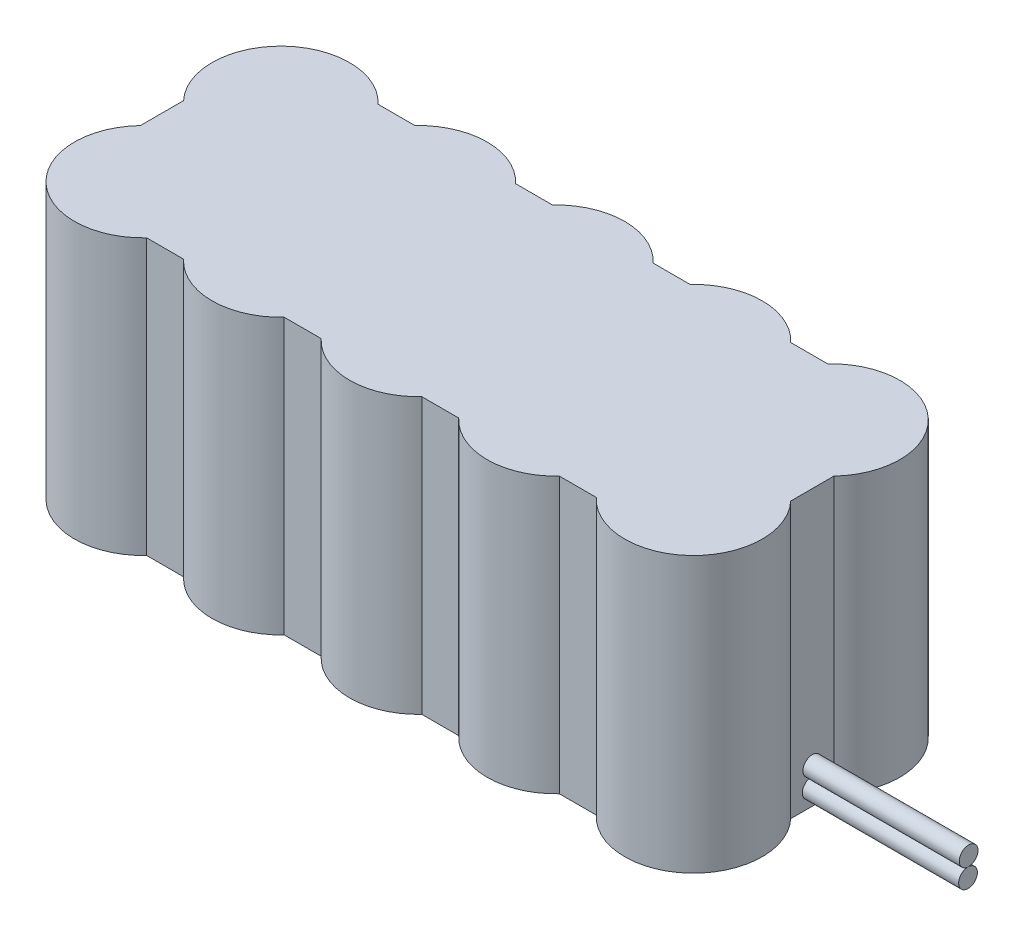
SolidWorks part; units mm, degrees
ref_plane "Front Plane" through (0, 0, 0) normal (0, 0, 1) x (1, 0, 0)
ref_plane "Top Plane" through (0, 0, 0) normal (0, 1, 0) x (1, 0, 0)
ref_plane "Right Plane" through (0, 0, 0) normal (1, 0, 0) x (0, 0, -1)
sketch "Sketch1" plane through (0, 0, 0) normal (0, 1, 0) x (1, 0, 0)
  circle A0 centre (0, 0) radius 11
  circle A1 centre (22, 0) radius 11
  circle A2 centre (44, 0) radius 11
  circle A3 centre (66, 0) radius 11
  circle A4 centre (88, 0) radius 11
  circle A5 centre (0, 22) radius 11
  circle A6 centre (22, 22) radius 11
  circle A7 centre (44, 22) radius 11
  circle A8 centre (66, 22) radius 11
  circle A9 centre (88, 22) radius 11
  dimension "D1" = 22
  dimension "D2" = 22
  dimension "D4" = 22
  dimension "D5" = 22
  dimension "D8" = 22
  dimension "D10" = 22
  dimension "D12" = 22
  dimension "D13" = 22
  dimension "D14" = 22
  dimension "D15" = 22
  dimension "D3" = 22
  dimension "D6" = 22
  dimension "D7" = 22
  dimension "D9" = 22
  dimension "D11" = 22
extrude "Extrude1" add sketch "Sketch1" along normal blind 44 contours A5 | A6 | A7 | A8 | A9 | A4 | A3 | A2 | A1 | A0
sketch "Sketch2" plane through (0, 44, 0) normal (0, 1, 0) x (1, 0, 0)
  line L1 (-8, 29.5) -> (96, 29.5)
  line L2 (-8, 29.5) -> (-8, -7.5)
  line L3 (-8, -7.5) -> (96, -7.5)
  line L4 (96, 29.5) -> (96, -7.5)
  circle A0 centre (0, 22) radius 11 construction
  circle A2 centre (88, 0) radius 11 construction
  dimension "D3" = 8
  dimension "D1" = 7.5
  dimension "D2" = 7.5
  dimension "D4" = 8
extrude "Extrude7" add sketch "Sketch2" against normal blind 44
sketch "Sketch4" plane through (96, 0, 0) normal (1, 0, 0) x (0, 0, -1)
  circle A1 centre (11, 5.6393) radius 1.5
  dimension "D2" = 3
extrude "Extrude12" add sketch "Sketch4" along normal blind 25
sketch "Sketch5" plane through (96, 0, 0) normal (1, 0, 0) x (0, 0, -1)
  circle A0 centre (10.9048, 2.6393) radius 1.5
  circle A1 centre (11, 5.6393) radius 1.5 construction
  dimension "D1" = 3
  dimension "D2" = 3
extrude "Extrude14" add sketch "Sketch5" along normal blind 25 separate body
sketch "Sketch6" plane through (0, 44, 0) normal (0, 1, 0) x (1, 0, 0)
  line L0 (-8, 11) -> (96, 11) construction
  line L1 (-8, 14.4502) -> (-8, 7.5498) construction
  line L2 (96, 7.5498) -> (96, 14.4502) construction
ref_plane "Plane1" through (0, 0, -11) normal (0, 0, 1) x (1, 0, 0)
